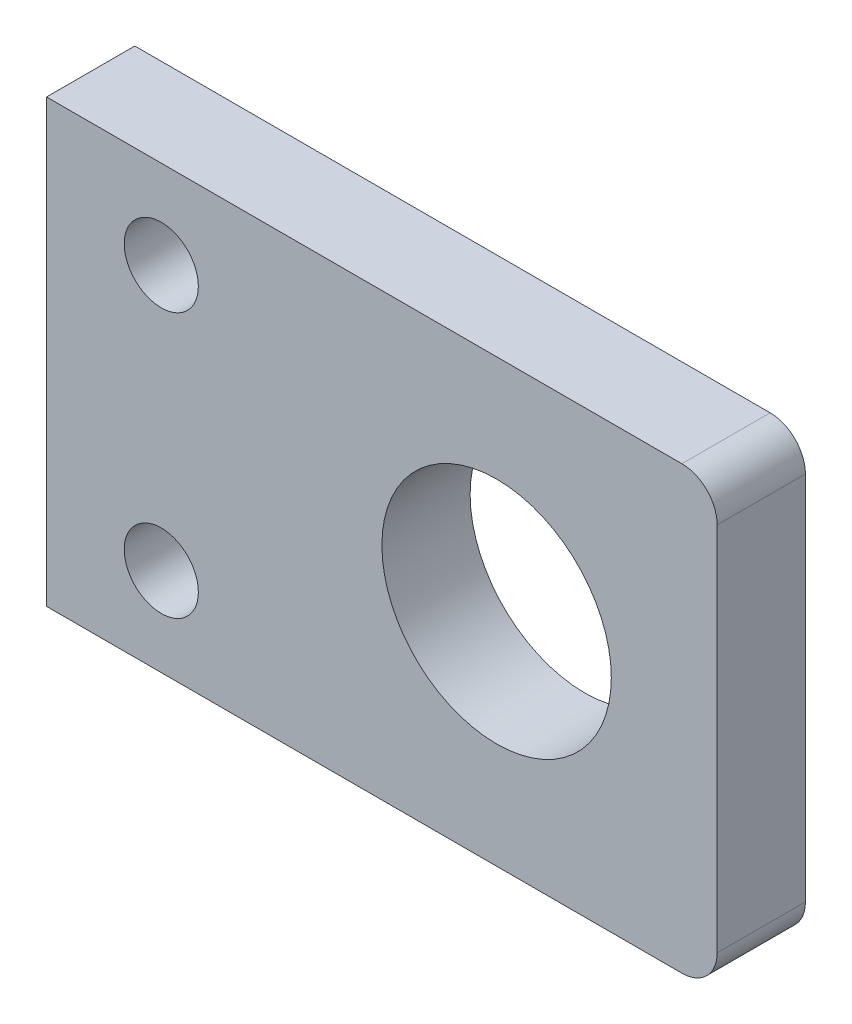
SolidWorks part; units mm, degrees
material "2014 合金"
ref_plane "前视基准面" through (0, 0, 0) normal (0, 0, 1) x (1, 0, 0)
ref_plane "上视基准面" through (0, 0, 0) normal (0, 1, 0) x (1, 0, 0)
ref_plane "右视基准面" through (0, 0, 0) normal (1, 0, 0) x (0, 0, -1)
other "Configuration Table"
sketch "草图1" plane through (0, 0, 0) normal (0, 0, 1) x (1, 0, 0)
  line L0 (-3.5155, 15.4686) -> (-3.5155, -7.4917)
  line L1 (-16.5155, 16.4184) -> (19.4845, 16.4184)
  line L2 (-16.5155, 16.4184) -> (-16.5155, -8.5816)
  line L3 (-16.5155, -8.5816) -> (19.4845, -8.5816)
  line L4 (21.4845, 14.4184) -> (21.4845, -6.5816)
  circle A0 centre (-10.0155, -3.5816) radius 2.1
  circle A1 centre (-10.0155, 11.4184) radius 2.1
  circle A2 centre (8.9845, 3.9184) radius 6.5
  arc A3 (19.4845, -8.5816) -> (21.4845, -6.5816) centre (19.4845, -6.5816) ccw
  arc A4 (19.4845, 16.4184) -> (21.4845, 14.4184) centre (19.4845, 14.4184) cw
  point P16 (21.4845, 16.4184)
  dimension "D3" = 4.2
  dimension "D4" = 4.2
  dimension "D9" = 13
  dimension "D10" = 13
  dimension "D13" = 2
  dimension "D1" = 25
  dimension "D2" = 38
  dimension "D5" = 5
  dimension "D6" = 6.5
  dimension "D7" = 6.5
  dimension "D8" = 15
  dimension "D11" = 25
  dimension "D12" = 12.5
  dimension "D14" = 12.5
  dimension "D15" = 5
extrude "凸台-拉伸1" add sketch "草图1" along normal blind 5
